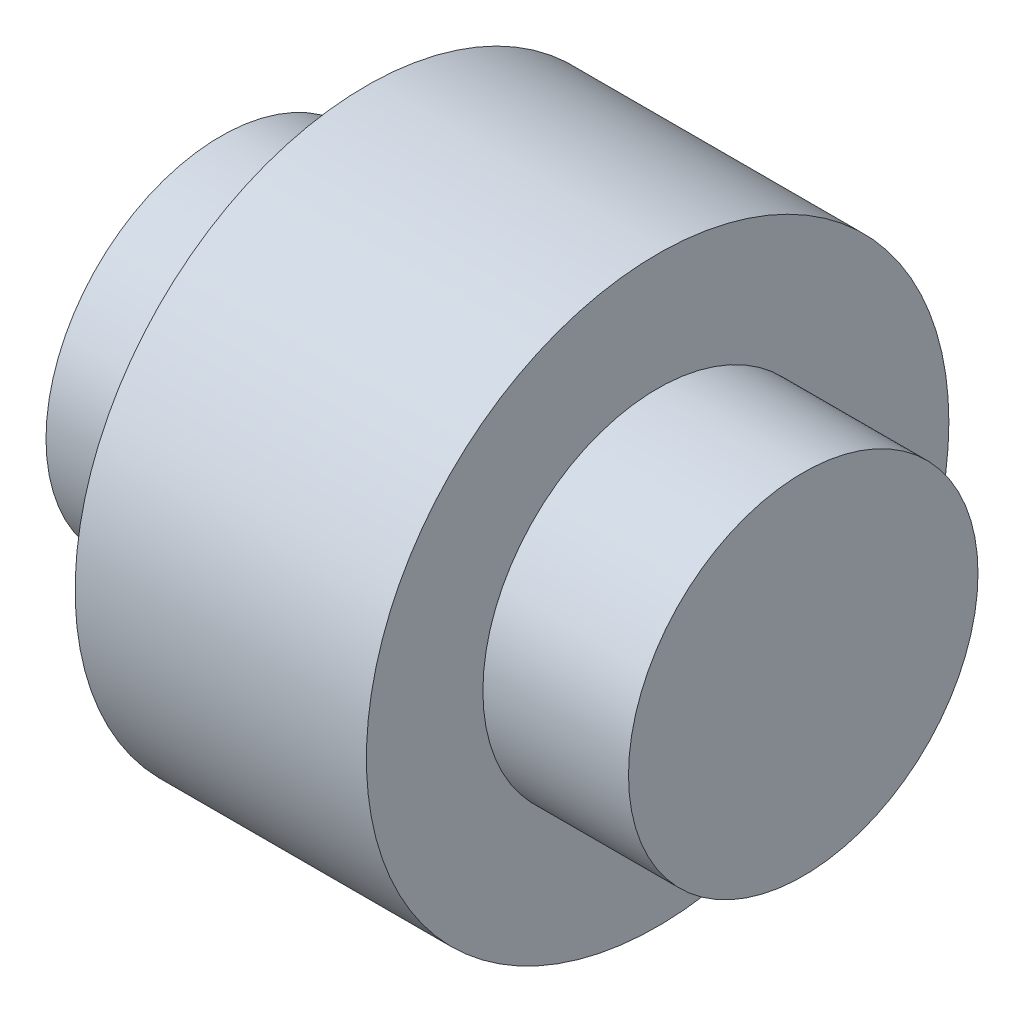
SolidWorks part; units mm, degrees
material "1.0035 (S185)"
ref_plane "Front Plane" through (0, 0, 0) normal (0, 0, 1) x (1, 0, 0)
ref_plane "Top Plane" through (0, 0, 0) normal (0, 1, 0) x (1, 0, 0)
ref_plane "Right Plane" through (0, 0, 0) normal (1, 0, 0) x (0, 0, -1)
sketch "Sketch1" plane through (0, 0, 0) normal (1, 0, 0) x (0, 0, -1)
  circle A0 centre (0, 0) radius 7.62
  dimension "D1" = 15.24
extrude "Boss-Extrude1" add sketch "Sketch1" against normal blind 25.4
ref_plane "Plane1" through (-12.7, 0, 0) normal (1, 0, 0) x (0, 0, -1)
sketch "Sketch2" plane through (-12.7, 0, 0) normal (1, 0, 0) x (0, 0, -1)
  circle A0 centre (0, 0) radius 12.7
  dimension "D1" = 25.4
extrude "Boss-Extrude2" add sketch "Sketch2" along normal mid plane 12.7
